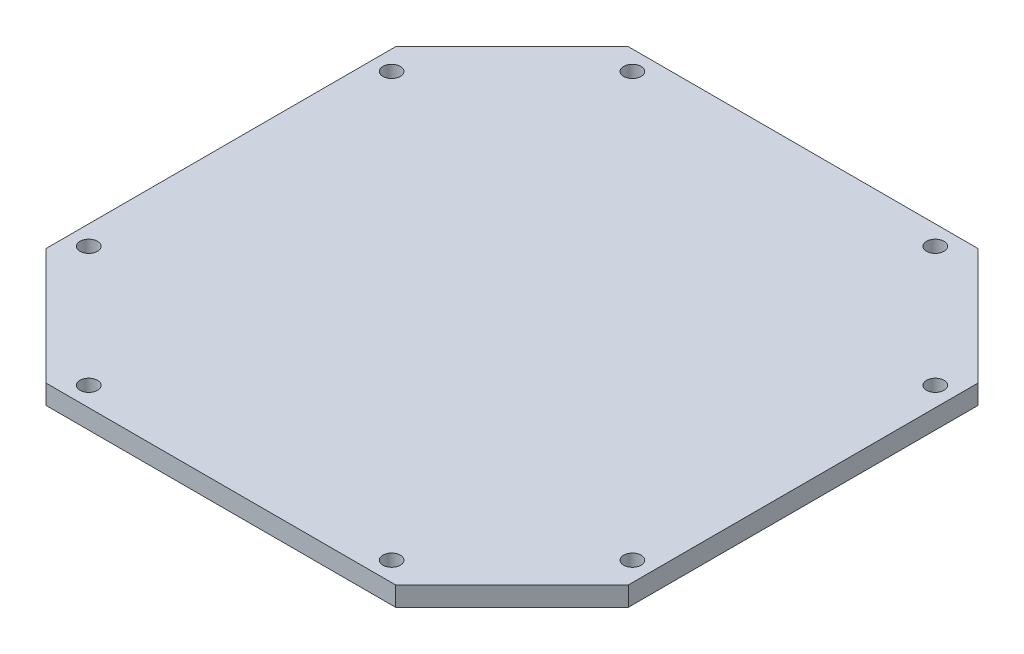
SolidWorks part; units mm, degrees
ref_plane "Front Plane" through (0, 0, 0) normal (0, 0, 1) x (1, 0, 0)
ref_plane "Top Plane" through (0, 0, 0) normal (0, 1, 0) x (1, 0, 0)
ref_plane "Right Plane" through (0, 0, 0) normal (1, 0, 0) x (0, 0, -1)
sketch "Sketch1" plane through (0, 0, 0) normal (0, 1, 0) x (1, 0, 0)
  line L0 (-90, 150) -> (-150, 90)
  line L1 (-150, -90) -> (150, -90)
  line L2 (-150, -90) -> (-150, 90)
  line L3 (-150, 90) -> (150, 90)
  line L4 (150, -90) -> (150, 90)
  line L5 (-150, -90) -> (150, 90) construction
  line L6 (-150, 90) -> (150, -90) construction
  line L7 (90, -150) -> (-90, -150)
  line L8 (90, -150) -> (90, 150)
  line L9 (90, 150) -> (-90, 150)
  line L10 (-90, -150) -> (-90, 150)
  line L11 (90, -150) -> (-90, 150) construction
  line L12 (90, 150) -> (-90, -150) construction
  line L13 (-150, -90) -> (-90, -150)
  line L14 (90, -150) -> (150, -90)
  line L15 (150, 90) -> (90, 150)
  point P0 (0, 0)
  point P5 (0, 0)
  dimension "D1" = 300
  dimension "D2" = 60
  dimension "D3" = 60
extrude "Boss-Extrude1" add sketch "Sketch1" along normal blind 10 contours L1 L10 L3 L2 | L1 L13 L10 | L3 L10 L0 | L10 L3 L8 L9 | L10 L1 L8 L3 | L10 L7 L8 L1 | L8 L14 L1 | L8 L1 L4 L3 | L3 L15 L8
sketch "Sketch2" plane through (0, 10, 0) normal (0, 1, 0) x (1, 0, 0)
  line L1 (140, -78) -> (-140, -78) construction
  line L2 (140, -78) -> (140, 78) construction
  line L3 (140, 78) -> (-140, 78) construction
  line L4 (-140, -78) -> (-140, 78) construction
  line L5 (140, -78) -> (-140, 78) construction
  line L6 (140, 78) -> (-140, -78) construction
  line L7 (-78, -140) -> (78, -140) construction
  line L8 (-78, -140) -> (-78, 140) construction
  line L9 (-78, 140) -> (78, 140) construction
  line L10 (78, -140) -> (78, 140) construction
  line L11 (-78, -140) -> (78, 140) construction
  line L12 (-78, 140) -> (78, -140) construction
  circle A0 centre (-78, 140) radius 4.5
  circle A1 centre (-140, 78) radius 4.5
  circle A2 centre (-140, -78) radius 4.5
  circle A3 centre (-78, -140) radius 4.5
  circle A4 centre (78, -140) radius 4.5
  circle A5 centre (140, -78) radius 4.5
  circle A6 centre (140, 78) radius 4.5
  circle A7 centre (78, 140) radius 4.5
  point P0 (0, 0)
  point P5 (0, 0)
  dimension "D4" = 9
  dimension "D1" = 280
  dimension "D2" = 62
  dimension "D3" = 62
extrude "Cut-Extrude1" cut sketch "Sketch2" against normal through all
